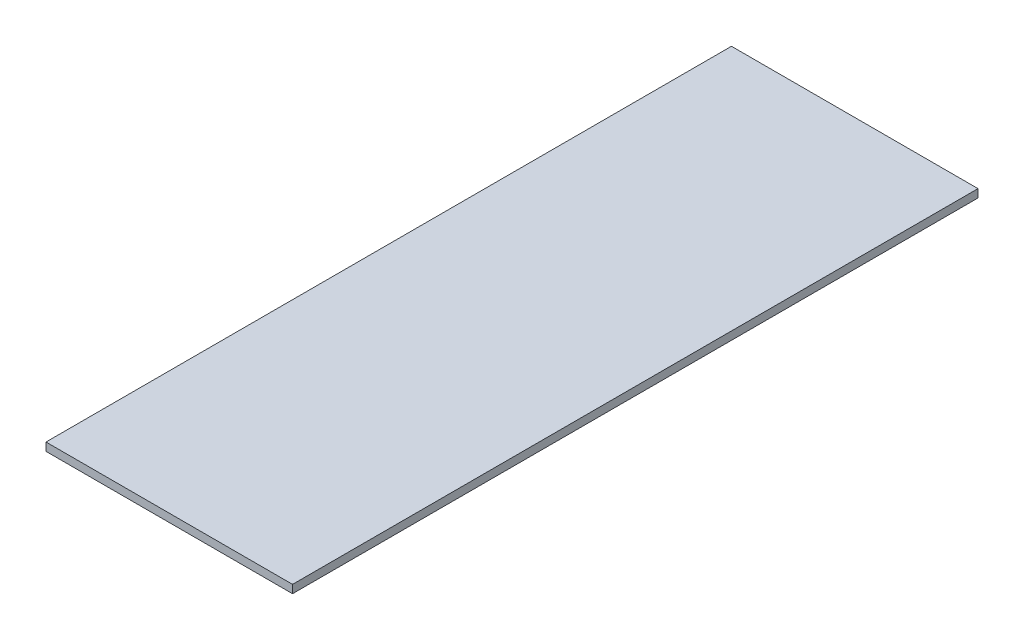
SolidWorks part; units mm, degrees
ref_plane "Front Plane" through (0, 0, 0) normal (0, 0, 1) x (1, 0, 0)
ref_plane "Top Plane" through (0, 0, 0) normal (0, 1, 0) x (1, 0, 0)
ref_plane "Right Plane" through (0, 0, 0) normal (1, 0, 0) x (0, 0, -1)
sketch "Sketch1" plane through (0, 0, 0) normal (0, 1, 0) x (1, 0, 0)
  line L1 (45.5, -113) -> (-45.5, -113)
  line L2 (45.5, -113) -> (45.5, 113)
  line L3 (45.5, 113) -> (-45.5, 113)
  line L4 (-45.5, -113) -> (-45.5, 113)
  line L5 (45.5, -113) -> (-45.5, 113) construction
  line L6 (45.5, 113) -> (-45.5, -113) construction
  point P0 (0, 0)
  dimension "D1" = 91
  dimension "D2" = 226
extrude "Boss-Extrude1" add sketch "Sketch1" along normal blind 3 separate body
other "Move Face1" face at (0, 1.5, 113) parameters "D1"=27
